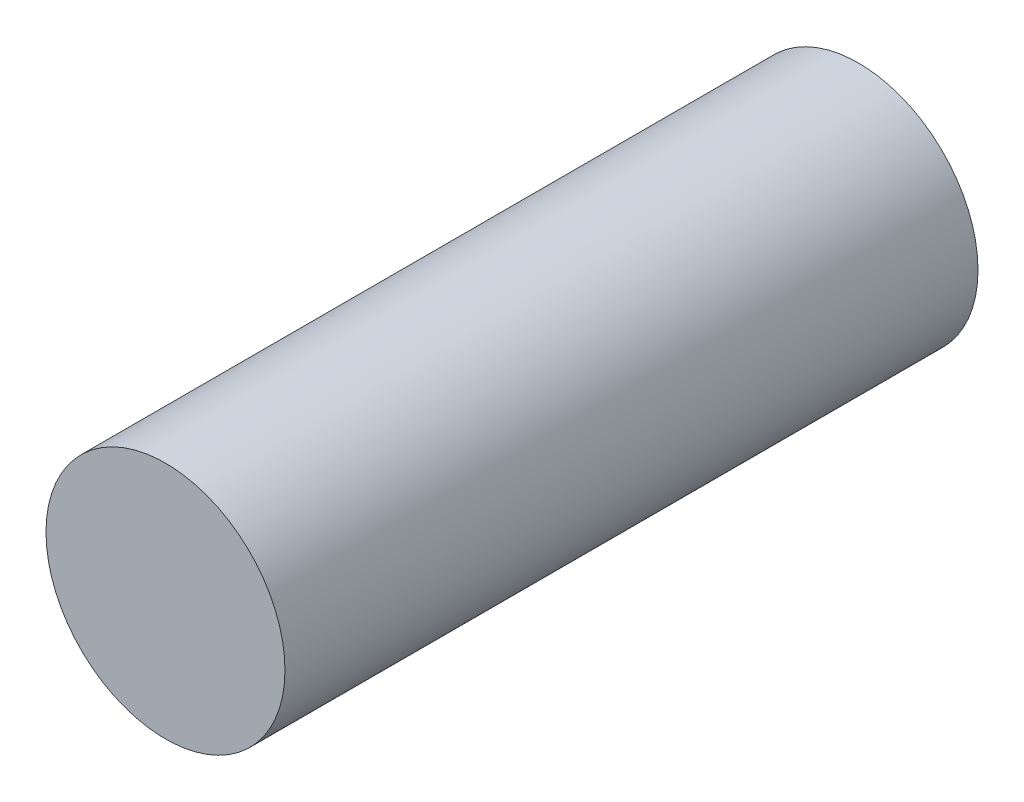
SolidWorks part; units mm, degrees
ref_plane "前视基准面" through (0, 0, 0) normal (0, 0, 1) x (1, 0, 0)
ref_plane "上视基准面" through (0, 0, 0) normal (0, 1, 0) x (1, 0, 0)
ref_plane "右视基准面" through (0, 0, 0) normal (1, 0, 0) x (0, 0, -1)
sketch "草图1" plane through (0, 0, 0) normal (0, 0, 1) x (1, 0, 0)
  circle A0 centre (0, 0) radius 2.5
  dimension "D1" = 5
extrude "凸台-拉伸1" add sketch "草图1" along normal blind 14.5
